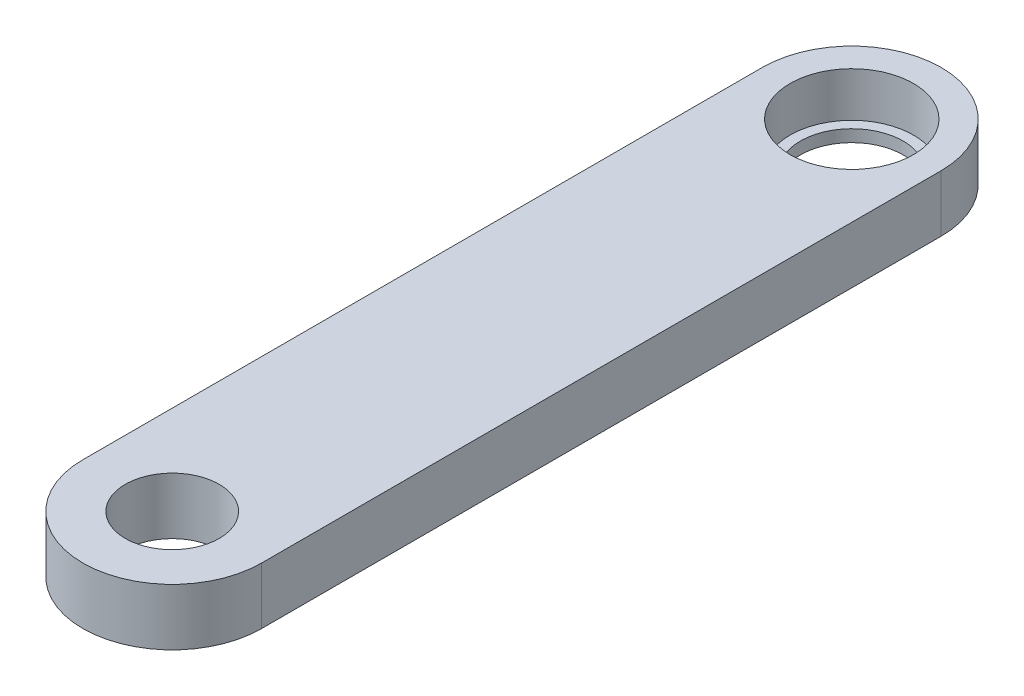
SolidWorks part; units mm, degrees
material "6061-T6 (SS)"
ref_plane "Front Plane" through (0, 0, 0) normal (0, 0, 1) x (1, 0, 0)
ref_plane "Top Plane" through (0, 0, 0) normal (0, 1, 0) x (1, 0, 0)
ref_plane "Right Plane" through (0, 0, 0) normal (1, 0, 0) x (0, 0, -1)
sketch "Sketch1" plane through (0, 0, 0) normal (0, 1, 0) x (1, 0, 0)
  line L1 (5, -19) -> (-5, -19)
  line L2 (5, -19) -> (5, 19)
  line L3 (5, 19) -> (-5, 19)
  line L4 (-5, -19) -> (-5, 19)
  line L5 (5, -19) -> (-5, 19) construction
  line L6 (5, 19) -> (-5, -19) construction
  arc A0 (-5, 19) -> (5, 19) centre (0, 19) cw
  arc A1 (-5, -19) -> (5, -19) centre (0, -19) ccw
  point P0 (0, 0)
  dimension "D1" = 10
  dimension "D2" = 38
extrude "Boss-Extrude1" add sketch "Sketch1" along normal mid plane 3.175 contours A0 L3 | L4 L1 L2 L3 | L1 A1
sketch "Sketch2" plane through (0, 1.5875, 0) normal (0, 1, 0) x (1, 0, 0)
  circle A0 centre (0, 19) radius 3.45
  dimension "D1" = 6.9
extrude "Cut-Extrude1" cut sketch "Sketch2" against normal blind 2.5
sketch "Sketch3" plane through (0, -0.9125, 0) normal (0, 1, 0) x (1, 0, 0)
  circle A0 centre (0, 19) radius 2.875
  dimension "D1" = 5.75
extrude "Cut-Extrude2" cut sketch "Sketch3" against normal through all
sketch "Sketch4" plane through (0, 1.5875, 0) normal (0, 1, 0) x (1, 0, 0)
  circle A0 centre (0, -19) radius 2.625
  dimension "D1" = 5.25
extrude "Cut-Extrude3" cut sketch "Sketch4" against normal through all
